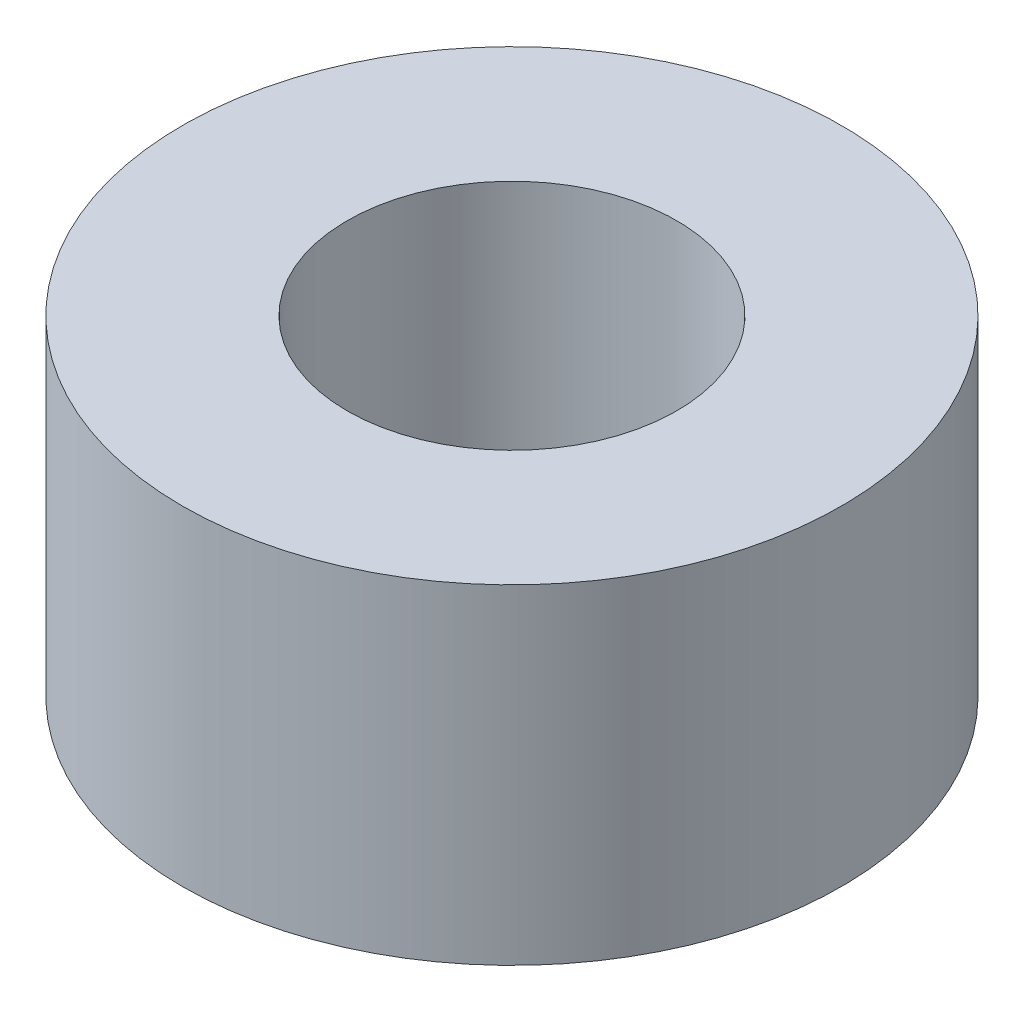
SolidWorks part; units mm, degrees
ref_plane "Front Plane" through (0, 0, 0) normal (0, 0, 1) x (1, 0, 0)
ref_plane "Top Plane" through (0, 0, 0) normal (0, 1, 0) x (1, 0, 0)
ref_plane "Right Plane" through (0, 0, 0) normal (1, 0, 0) x (0, 0, -1)
sketch "Sketch1" plane through (0, 0, 0) normal (0, 1, 0) x (1, 0, 0)
  circle A0 centre (0, 0) radius 3
  circle A1 centre (0, 0) radius 1.5
  dimension "D1" = 6
  dimension "D2" = 3
extrude "Boss-Extrude1" add sketch "Sketch1" along normal blind 3
